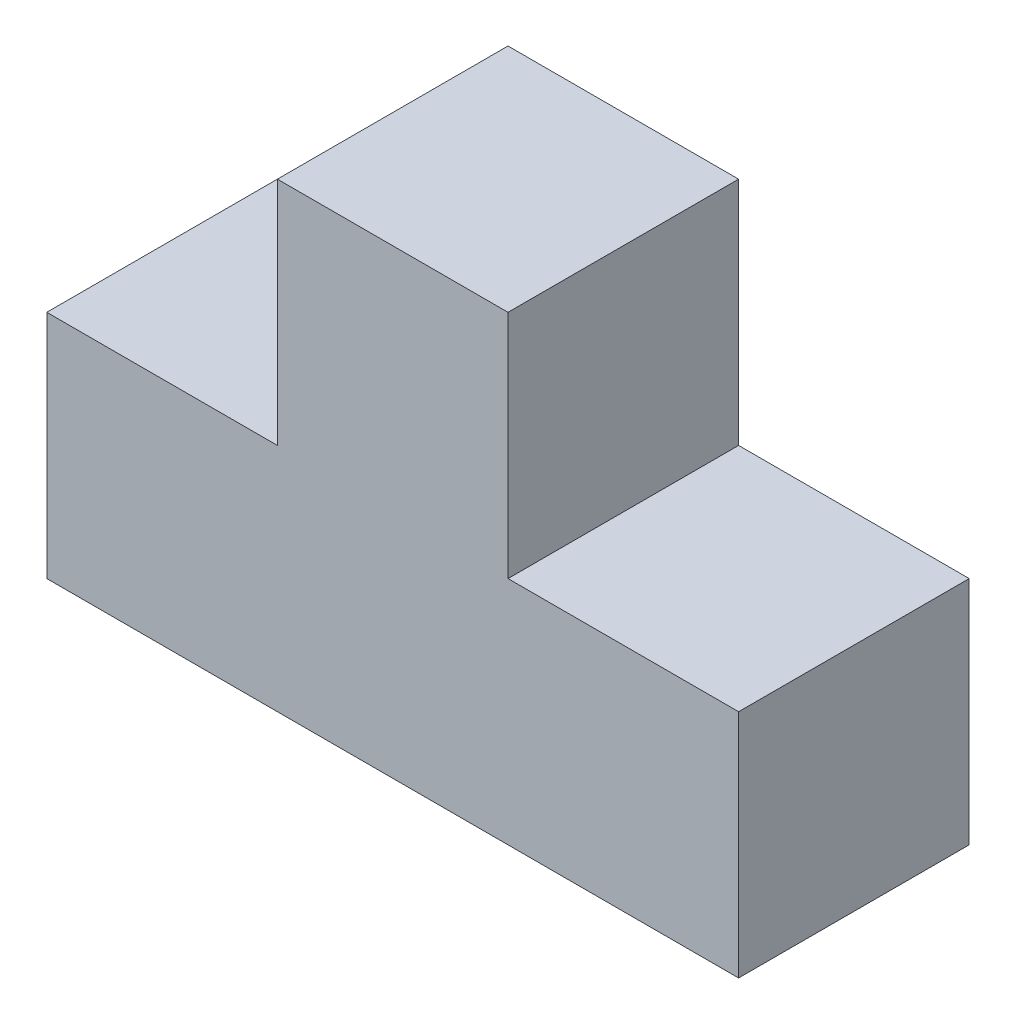
SolidWorks part; units mm, degrees
material "A286 Iron Base Superalloy"
ref_plane "Front Plane" through (0, 0, 0) normal (0, 0, 1) x (1, 0, 0)
ref_plane "Top Plane" through (0, 0, 0) normal (0, 1, 0) x (1, 0, 0)
ref_plane "Right Plane" through (0, 0, 0) normal (1, 0, 0) x (0, 0, -1)
sketch "Sketch1" plane through (0, 0, 0) normal (0, 0, 1) x (1, 0, 0)
  line L0 (0, 0) -> (90, 0)
  line L1 (90, 0) -> (90, 30)
  line L2 (90, 30) -> (60, 30)
  line L3 (60, 30) -> (60, 60)
  line L4 (60, 60) -> (30, 60)
  line L5 (30, 60) -> (30, 30)
  line L6 (30, 30) -> (0, 30)
  line L7 (0, 30) -> (0, 0)
  dimension "D1" = 90
  dimension "D2" = 30
  dimension "D3" = 30
  dimension "D4" = 30
  dimension "D5" = 30
  dimension "D6" = 30
  dimension "D7" = 30
extrude "Boss-Extrude1" add sketch "Sketch1" along normal blind 30
